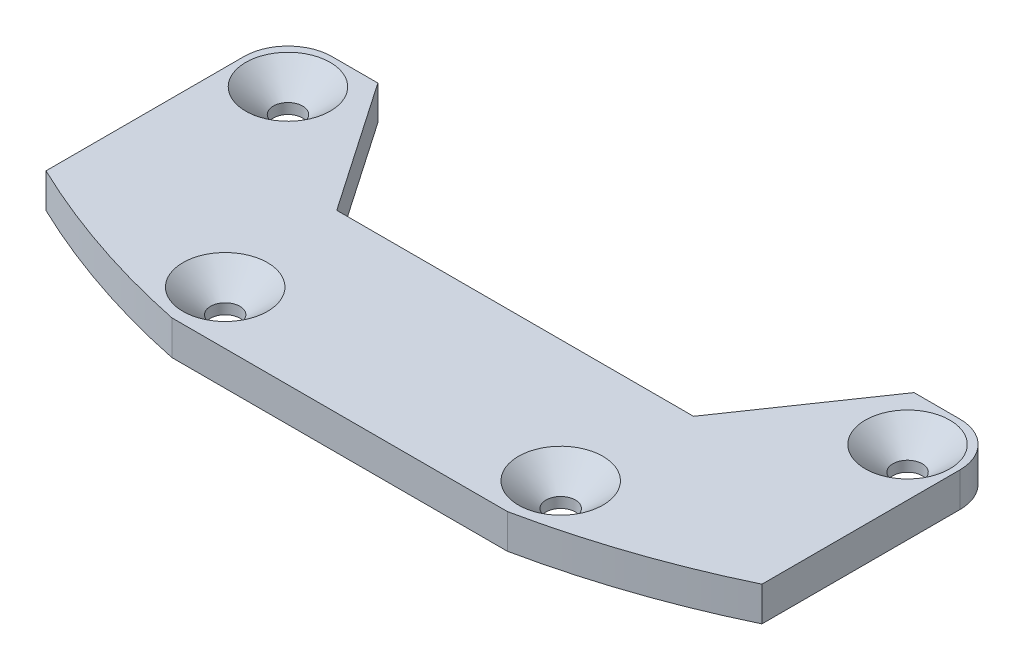
SolidWorks part; units mm, degrees
material "6061 Alloy"
ref_plane "Front Plane" through (0, 0, 0) normal (0, 0, 1) x (1, 0, 0)
ref_plane "Top Plane" through (0, 0, 0) normal (0, 1, 0) x (1, 0, 0)
ref_plane "Right Plane" through (0, 0, 0) normal (1, 0, 0) x (0, 0, -1)
sketch "Sketch1" plane through (0, 0, 0) normal (0, 1, 0) x (1, 0, 0)
  line L0 (-24.7301, 14.1288) -> (-16.4543, 2.0638)
  line L1 (-33.02, -14.1287) -> (-15.473, -14.1287) construction
  line L2 (-33.02, -14.1287) -> (-33.02, -8.1903) construction
  line L3 (-28.956, 14.1288) -> (-24.7301, 14.1288)
  line L4 (33.02, -14.1287) -> (33.02, -8.1903) construction
  line L5 (-33.02, -14.1287) -> (33.02, 14.1288) construction
  line L6 (-33.02, 14.1288) -> (33.02, -14.1287) construction
  line L7 (-16.4543, 2.0638) -> (16.4543, 2.0638)
  line L8 (0, -1000) -> (0, 49000) construction
  line L9 (24.7301, 14.1288) -> (16.4543, 2.0638)
  line L10 (24.7301, 14.1288) -> (28.956, 14.1288)
  line L11 (-33.02, -8.1903) -> (-33.02, 10.0648)
  line L12 (33.02, -8.1903) -> (33.02, 10.0648)
  line L13 (-15.473, -14.1287) -> (15.473, -14.1287)
  line L14 (15.473, -14.1287) -> (33.02, -14.1287) construction
  arc A0 (28.956, 14.1288) -> (33.02, 10.0648) centre (28.956, 10.0648) cw
  arc A1 (-33.02, 10.0648) -> (-28.956, 14.1288) centre (-28.956, 10.0648) cw
  arc A4 (33.02, -8.1903) -> (15.473, -14.1287) centre (0, 60.4838) cw
  circle A5 centre (-28.575, 9.6837) radius 1.3526
  circle A6 centre (-15.473, -9.2075) radius 1.3525
  circle A9 centre (15.473, -9.2075) radius 1.3526
  circle A10 centre (28.575, 9.6837) radius 1.3526
  arc A11 (-15.473, -14.1287) -> (-33.02, -8.1903) centre (0, 60.4838) cw
  point P0 (0, 0)
  point P20 (0, 2.0638)
  dimension "D3" = 4.064
  dimension "D1" = 28.2575
  dimension "D2" = 66.04
extrude "Boss-Extrude1" add sketch "Sketch1" along normal blind 3.175
chamfer "Chamfer2" distance 2.5464 angle 41 4 edges at (-28.575, 3.175, -8.3312) (-15.473, 3.175, 10.5601) (15.473, 3.175, 7.8549) (28.575, 3.175, -11.0363)
